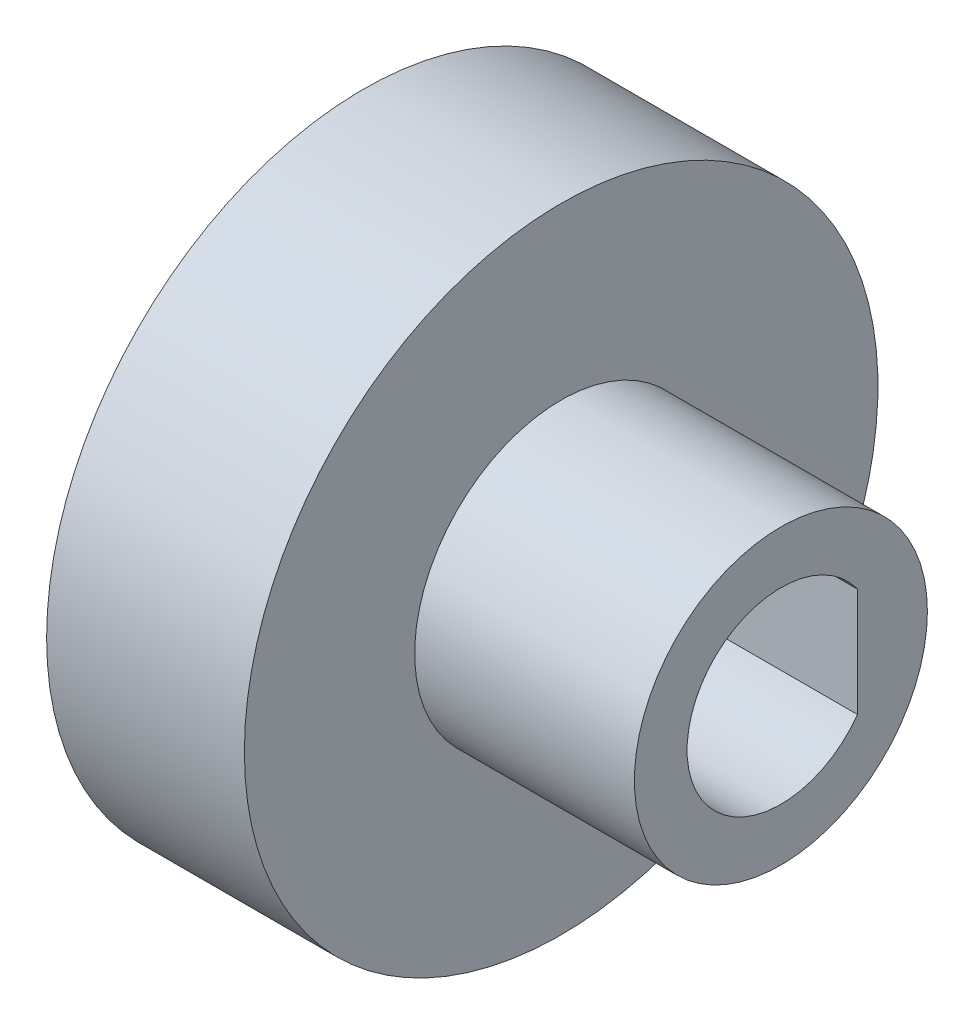
SolidWorks part; units mm, degrees
ref_plane "Front Plane" through (0, 0, 0) normal (0, 0, 1) x (1, 0, 0)
ref_plane "Top Plane" through (0, 0, 0) normal (0, 1, 0) x (1, 0, 0)
ref_plane "Right Plane" through (0, 0, 0) normal (1, 0, 0) x (0, 0, -1)
sketch "Sketch1" plane through (0, 0, 0) normal (1, 0, 0) x (0, 0, -1)
  circle A0 centre (0, 0) radius 5.08
  dimension "D1" = 10.16
extrude "Boss-Extrude1" add sketch "Sketch1" along normal blind 7.62
sketch "Sketch2" plane through (0, 0, 0) normal (-1, 0, 0) x (0, 0, 1)
  circle A0 centre (0, 0) radius 10.9855
  dimension "D1" = 21.971
extrude "Boss-Extrude2" add sketch "Sketch2" along normal blind 6.858
sketch "Sketch3" plane through (-6.858, 0, 0) normal (-1, 0, 0) x (0, 0, 1)
  line L0 (-2.4, -1.8) -> (-2.4, 1.8) construction
  line L1 (-2.4, -1.8) -> (-2.4, 1.8) construction
  line L2 (-2.654, -1.8828) -> (-2.654, 1.8828)
  arc A0 (-2.4, -1.8) -> (-2.4, 1.8) centre (0, 0) ccw construction
  arc A1 (-2.4, -1.8) -> (-2.4, 1.8) centre (0, 0) ccw construction
  arc A2 (-2.654, -1.8828) -> (-2.654, 1.8828) centre (0, 0) ccw
  dimension "D1" = 0.254
extrude "Cut-Extrude1" cut sketch "Sketch3" against normal up to next
